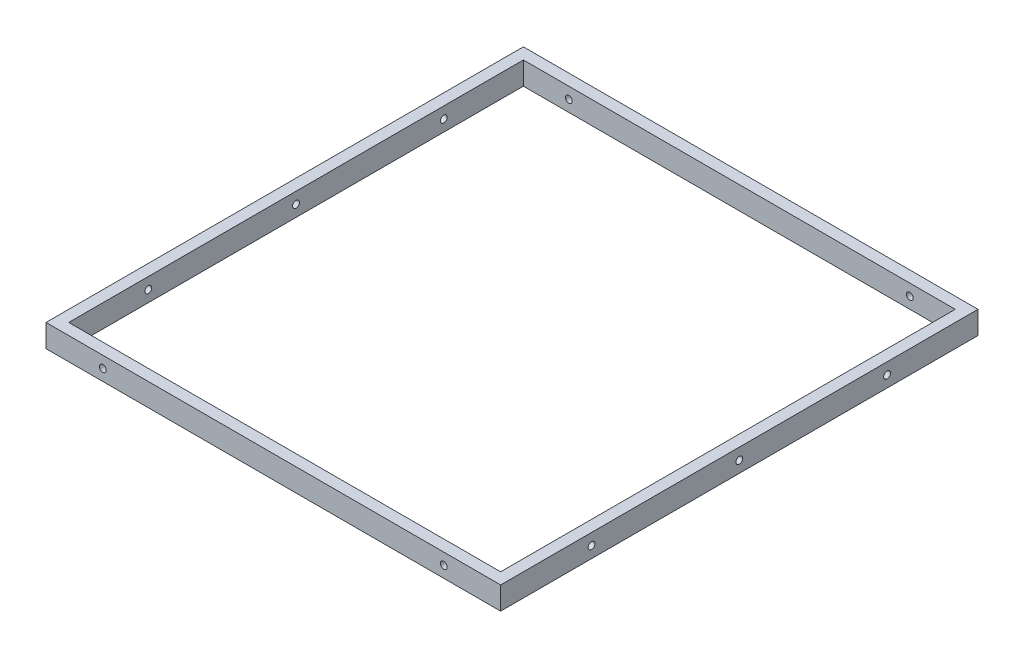
SolidWorks part; units mm, degrees
ref_plane "Front Plane" through (0, 0, 0) normal (0, 0, 1) x (1, 0, 0)
ref_plane "Top Plane" through (0, 0, 0) normal (0, 1, 0) x (1, 0, 0)
ref_plane "Right Plane" through (0, 0, 0) normal (1, 0, 0) x (0, 0, -1)
sketch "Sketch1" plane through (0, 0, 0) normal (0, 1, 0) x (1, 0, 0)
  line L0 (-200, 210) -> (200, 210)
  line L1 (-190, -200) -> (190, -200)
  line L2 (-190, -200) -> (-190, 200)
  line L3 (-190, 200) -> (190, 200)
  line L4 (190, -200) -> (190, 200)
  line L5 (-190, -200) -> (190, 200) construction
  line L6 (-190, 200) -> (190, -200) construction
  line L7 (200, -210) -> (200, 210)
  line L8 (-200, -210) -> (200, -210)
  line L9 (-200, -210) -> (-200, 210)
  point P0 (0, 0)
  dimension "D1" = 380
  dimension "D2" = 400
  dimension "D3" = 10
extrude "Boss-Extrude1" add sketch "Sketch1" along normal blind 20
sketch "Sketch2" plane through (-200, 0, 0) normal (-1, 0, 0) x (0, 0, 1)
  circle A0 centre (0, 10) radius 3
  circle A1 centre (130, 10) radius 3
  circle A2 centre (-130, 10) radius 3
  dimension "D1" = 10
  dimension "D2" = 2
  dimension "D3" = 2
extrude "Cut-Extrude1" cut sketch "Sketch2" against normal up to surface (400 mm away) up to face at (200, 10, 0)
sketch "Sketch3" plane through (0, 0, -210) normal (0, 0, -1) x (-1, 0, 0)
  line L0 (-200, 0) -> (200, 0) construction
  circle A0 centre (-150, 10) radius 3
  circle A1 centre (150, 10) radius 3
  dimension "D1" = 10
  dimension "D2" = 150
  dimension "D3" = 2
extrude "Cut-Extrude2" cut sketch "Sketch3" against normal up to surface (420 mm away) up to face at (0, 10, 210)
